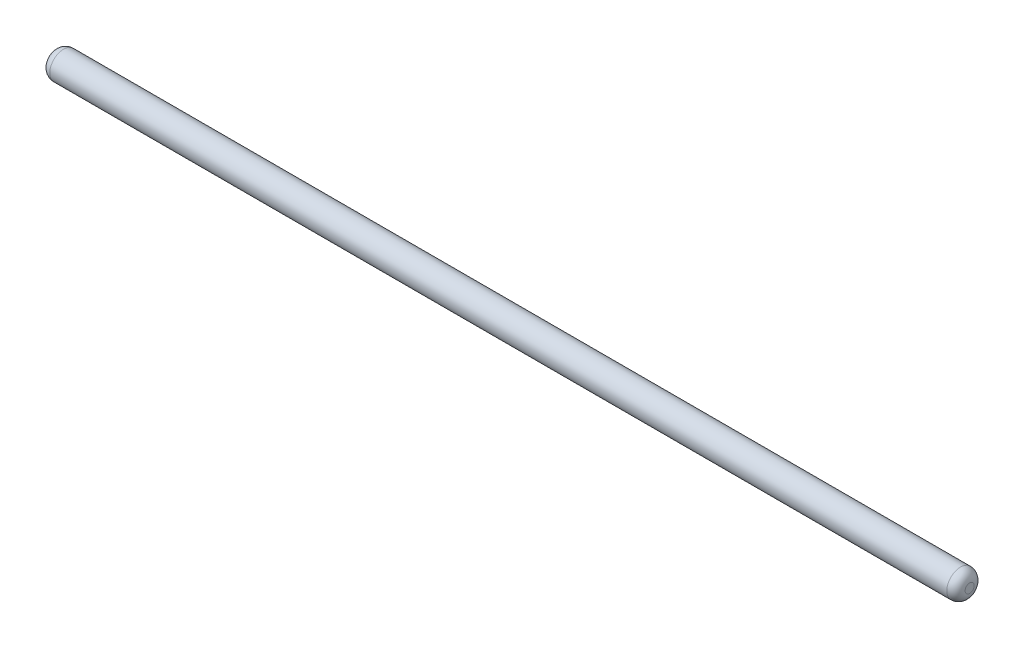
SolidWorks part; units mm, degrees
ref_plane "Piano frontale" through (0, 0, 0) normal (0, 0, 1) x (1, 0, 0)
ref_plane "Piano superiore" through (0, 0, 0) normal (0, 1, 0) x (1, 0, 0)
ref_plane "Piano destro" through (0, 0, 0) normal (1, 0, 0) x (0, 0, -1)
sketch "Schizzo2" plane through (0, 0, 0) normal (0, 0, 1) x (1, 0, 0)
  line L5 (0, 0) -> (100, 0)
  line L6 (0, 0) -> (0, 0.5)
  line L7 (1, 1.5) -> (99, 1.5)
  line L8 (100, 0) -> (100, 0.5)
  arc A2 (99, 1.5) -> (100, 0.5) centre (99, 0.5) cw
  arc A3 (0, 0.5) -> (1, 1.5) centre (1, 0.5) cw
  dimension "D4" = 1
  dimension "D2" = 100
  dimension "D3" = 1.5
revolve "Rivoluzione1" add sketch "Schizzo2" angle 360 about L5
equation "\"D\"= 3mm"
equation "\"c\"= 100mm"
equation "\"D2@Schizzo2\"=\"c\""
equation "\"D3@Schizzo2\"=\"D\"/2"
equation "\"D4@Schizzo2\"=\"D\"/3"
